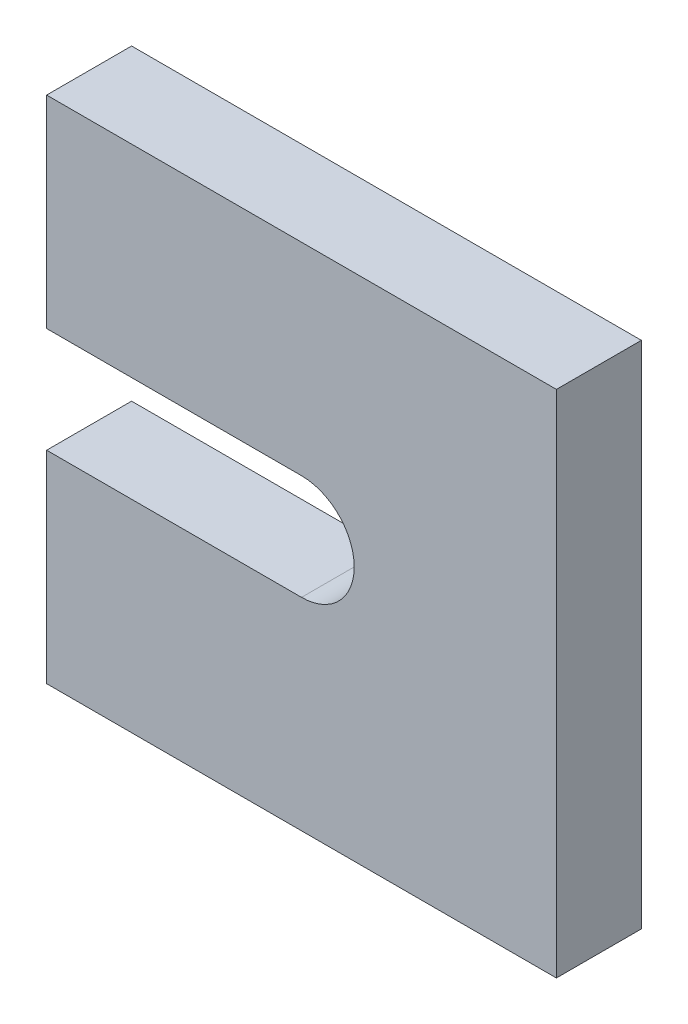
SolidWorks part; units mm, degrees
ref_plane "Front Plane" through (0, 0, 0) normal (0, 0, 1) x (1, 0, 0)
ref_plane "Top Plane" through (0, 0, 0) normal (0, 1, 0) x (1, 0, 0)
ref_plane "Right Plane" through (0, 0, 0) normal (1, 0, 0) x (0, 0, -1)
sketch "Sketch1" plane through (0, 0, 0) normal (0, 0, 1) x (1, 0, 0)
  line L0 (15, 18.1) -> (0, 18.1)
  line L1 (0, 0) -> (30, 0)
  line L2 (0, 0) -> (0, 11.9)
  line L3 (0, 30) -> (30, 30)
  line L4 (30, 0) -> (30, 30)
  line L5 (15, 11.9) -> (0, 11.9)
  line L6 (0, 18.1) -> (0, 30)
  arc A0 (15, 11.9) -> (15, 18.1) centre (15, 15) ccw
  dimension "D3" = 6.2
  dimension "D1" = 30
  dimension "D2" = 30
extrude "Boss-Extrude1" add sketch "Sketch1" along normal blind 5
